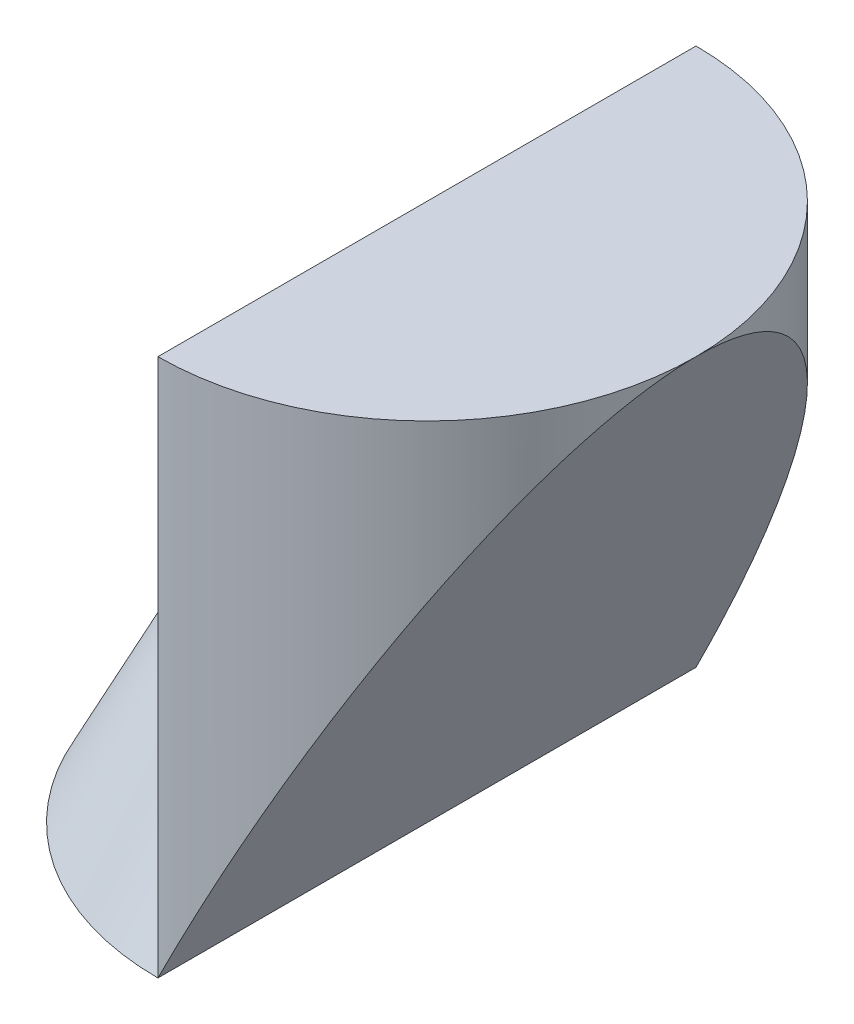
SolidWorks part; units mm, degrees
ref_plane "Front" through (0, 0, 0) normal (0, 0, 1) x (1, 0, 0)
ref_plane "Top" through (0, 0, 0) normal (0, 1, 0) x (1, 0, 0)
ref_plane "Right" through (0, 0, 0) normal (1, 0, 0) x (0, 0, -1)
sketch "Sketch1" plane through (0, 0, 0) normal (0, 1, 0) x (1, 0, 0)
  line L0 (2, 0) -> (2, -4)
  arc A0 (2, 0) -> (2, -4) centre (2, -2) cw
extrude "Boss-Extrude1" add sketch "Sketch1" along normal blind 4
sketch "Sketch6" plane through (2, 0, 0) normal (-1, 0, 0) x (0, 0, 1)
  line L0 (2, 4) -> (2, 3.3088) construction
  line L1 (0, 4) -> (4, 4) construction
  line L2 (2, 0) -> (2, 4)
  line L3 (0, 0) -> (4, 0) construction
  line L4 (2, 4) -> (4, 0)
  line L5 (4, 0) -> (2, 0)
revolve "Revolve1" add sketch "Sketch6" angle 180 about L2
sketch "Sketch7" plane through (0, 0, 0) normal (0, 0, 1) x (1, 0, 0)
  line L0 (2, 0) -> (4, 4)
  line L1 (4, 4) -> (4, 0)
  line L2 (4, 0) -> (2, 0)
extrude "Cut-Extrude4" cut sketch "Sketch7" along normal blind 4 contours L2 L1 L0
